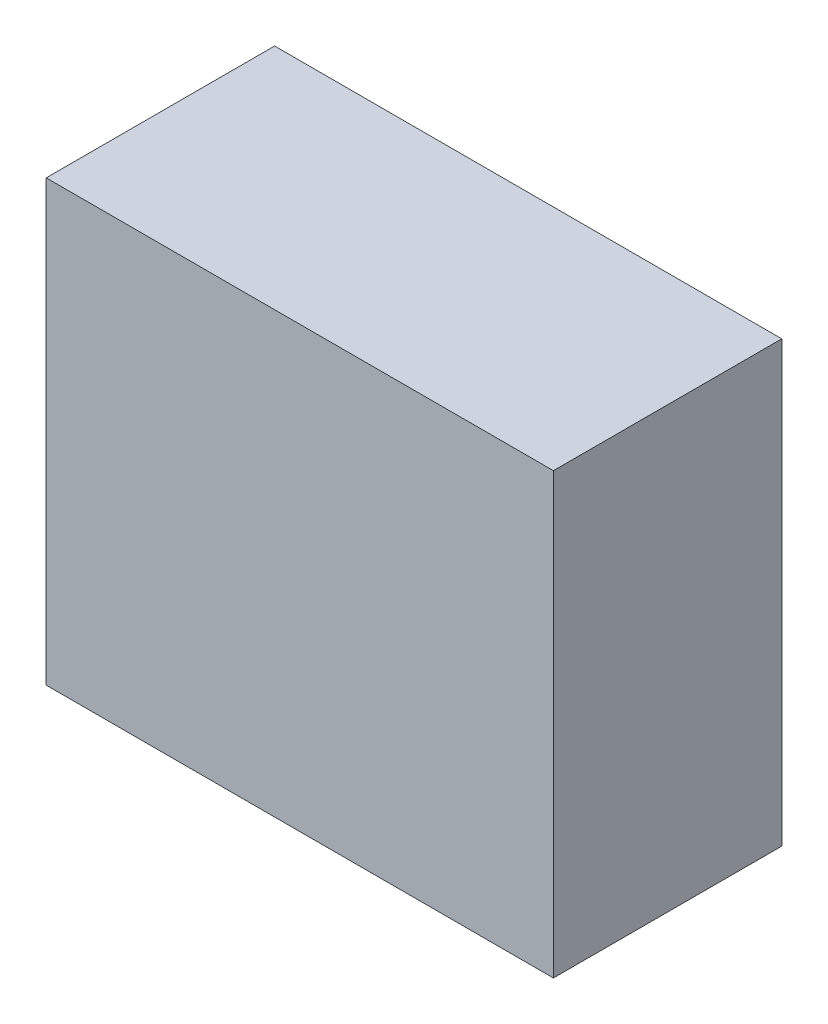
SolidWorks part; units mm, degrees
ref_plane "Front Plane" through (0, 0, 0) normal (0, 0, 1) x (1, 0, 0)
ref_plane "Top Plane" through (0, 0, 0) normal (0, 1, 0) x (1, 0, 0)
ref_plane "Right Plane" through (0, 0, 0) normal (1, 0, 0) x (0, 0, -1)
sketch "Sketch1" plane through (0, 0, 0) normal (0, 1, 0) x (1, 0, 0)
  line L1 (-22.225, -10.0076) -> (22.225, -10.0076)
  line L2 (-22.225, -10.0076) -> (-22.225, 10.0076)
  line L3 (-22.225, 10.0076) -> (22.225, 10.0076)
  line L4 (22.225, -10.0076) -> (22.225, 10.0076)
  line L5 (-22.225, -10.0076) -> (22.225, 10.0076) construction
  line L6 (-22.225, 10.0076) -> (22.225, -10.0076) construction
  point P0 (0, 0)
  dimension "D1" = 44.45
  dimension "D2" = 20.0152
extrude "Boss-Extrude1" add sketch "Sketch1" along normal blind 38.5064
